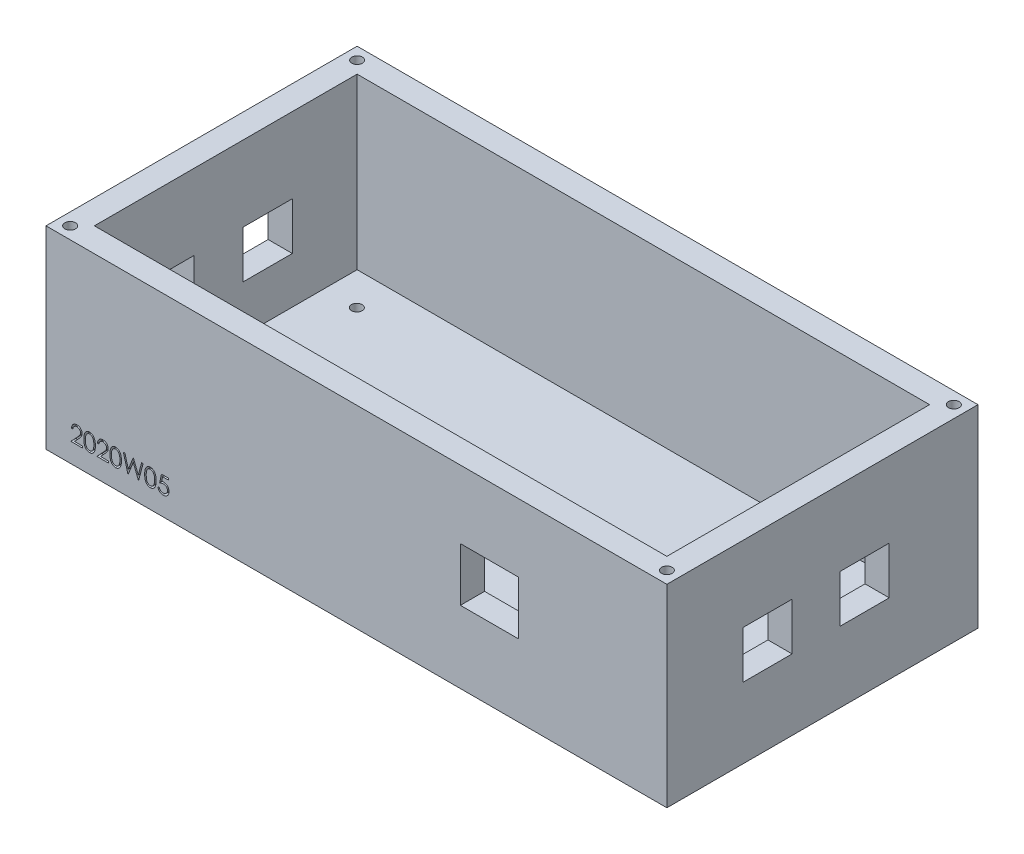
SolidWorks part; units mm, degrees
ref_plane "Front Plane" through (0, 0, 0) normal (0, 0, 1) x (1, 0, 0)
ref_plane "Top Plane" through (0, 0, 0) normal (0, 1, 0) x (1, 0, 0)
ref_plane "Right Plane" through (0, 0, 0) normal (1, 0, 0) x (0, 0, -1)
sketch "Sketch1" plane through (0, 0, 0) normal (0, 1, 0) x (1, 0, 0)
  line L0 (0, 0) -> (-128.3, 0)
  line L1 (-128.3, 0) -> (-128.3, 64.29)
  line L2 (-128.3, 64.29) -> (0, 64.29)
  line L3 (0, 64.29) -> (0, 0)
  dimension "D1" = 128.3
  dimension "D2" = 64.29
extrude "Boss-Extrude1" add sketch "Sketch1" along normal blind 5
sketch "Sketch2" plane through (0, 5, 0) normal (0, 1, 0) x (1, 0, 0)
  line L0 (-128.3, 64.29) -> (-128.3, 0)
  line L1 (-128.3, 0) -> (0, 0)
  line L2 (0, 0) -> (0, 64.29)
  line L3 (0, 64.29) -> (-128.3, 64.29)
  line L4 (-123.3, 59.29) -> (-123.3, 5)
  line L5 (-123.3, 5) -> (-5, 5)
  line L6 (-5, 5) -> (-5, 59.29)
  line L7 (-5, 59.29) -> (-123.3, 59.29)
  line L8 (-123.3, 59.29) -> (-123.3, 64.29) construction
  line L9 (-123.3, 59.29) -> (-128.3, 59.29) construction
  line L10 (-5, 59.29) -> (0, 59.29) construction
  line L11 (-5, 5) -> (-5, 0) construction
  dimension "D1" = 5
  dimension "D2" = 5
extrude "Boss-Extrude2" add sketch "Sketch2" along normal blind 35
sketch "Sketch3" plane through (0, 5, 0) normal (0, 1, 0) x (1, 0, 0)
  line L0 (-116.54, 52.465) -> (-11.76, 52.465) construction
  line L1 (-11.76, 52.465) -> (-11.76, 11.825) construction
  line L2 (-11.76, 11.825) -> (-116.54, 11.825) construction
  line L3 (-116.54, 11.825) -> (-116.54, 52.465) construction
  line L4 (-123.3, 52.465) -> (-116.54, 52.465) construction
  line L5 (-123.3, 59.29) -> (-123.3, 5) construction
  line L6 (-116.54, 52.465) -> (-116.54, 59.29) construction
  line L7 (-5, 59.29) -> (-123.3, 59.29) construction
  line L8 (-11.76, 52.465) -> (-5, 52.465) construction
  line L9 (-5, 5) -> (-5, 59.29) construction
  line L10 (-116.54, 11.825) -> (-116.54, 5) construction
  line L11 (-123.3, 5) -> (-5, 5) construction
  circle A0 centre (-116.54, 52.465) radius 1.1
  circle A1 centre (-11.76, 52.465) radius 1.1
  circle A2 centre (-11.76, 11.825) radius 1.1
  circle A3 centre (-116.54, 11.825) radius 1.1
  dimension "D1" = 2.2
  dimension "D2" = 104.78
  dimension "D3" = 40.64
extrude "Cut-Extrude1" cut sketch "Sketch3" against normal through all
sketch "Sketch4" plane through (0, 40, 0) normal (0, 1, 0) x (1, 0, 0)
  line L0 (-2.5, 61.79) -> (-125.8, 61.79) construction
  line L1 (-125.8, 61.79) -> (-125.8, 2.5) construction
  line L2 (-125.8, 2.5) -> (-2.5, 2.5) construction
  line L3 (-2.5, 2.5) -> (-2.5, 61.79) construction
  line L4 (-123.3, 59.29) -> (-125.8, 59.29) construction
  line L5 (-125.8, 59.29) -> (-128.3, 59.29) construction
  line L6 (-128.3, 64.29) -> (-128.3, 0) construction
  line L7 (-5, 59.29) -> (-2.5, 59.29) construction
  line L8 (-5, 5) -> (-5, 59.29) construction
  line L9 (-5, 5) -> (-5, 59.29) construction
  line L10 (-2.5, 59.29) -> (0, 59.29) construction
  line L11 (0, 0) -> (0, 64.29) construction
  line L12 (-123.3, 59.29) -> (-123.3, 61.79) construction
  line L13 (-123.3, 61.79) -> (-123.3, 64.29) construction
  line L14 (0, 64.29) -> (-128.3, 64.29) construction
  line L15 (-123.3, 5) -> (-123.3, 2.5) construction
  line L16 (-123.3, 2.5) -> (-123.3, 0) construction
  line L17 (-128.3, 0) -> (0, 0) construction
  circle A0 centre (-125.8, 61.79) radius 1.1
  circle A1 centre (-125.8, 2.5) radius 1.1
  circle A2 centre (-2.5, 2.5) radius 1.1
  circle A3 centre (-2.5, 61.79) radius 1.1
  dimension "D1" = 2.2
extrude "Cut-Extrude2" cut sketch "Sketch4" against normal blind 5
sketch "Sketch5" plane through (-128.3, 0, 0) normal (-1, 0, 0) x (0, 0, 1)
  line L0 (-45.9, 24.4) -> (-45.9, 14.6)
  line L1 (-45.9, 14.6) -> (-35.74, 14.6)
  line L2 (-35.74, 14.6) -> (-35.74, 24.4)
  line L3 (-35.74, 24.4) -> (-45.9, 24.4)
  line L4 (-25.58, 24.4) -> (-25.58, 14.6)
  line L5 (-25.58, 14.6) -> (-15.42, 14.6)
  line L6 (-15.42, 14.6) -> (-15.42, 24.4)
  line L7 (-25.58, 24.4) -> (-15.42, 24.4)
  line L8 (-64.29, 40) -> (-64.29, 0) construction
  line L9 (-64.29, 0) -> (0, 0) construction
  dimension "D1" = 10.16
  dimension "D2" = 10.16
  dimension "D3" = 10.16
  dimension "D4" = 18.39
  dimension "D5" = 9.8
  dimension "D6" = 14.6
extrude "Cut-Extrude3" cut sketch "Sketch5" against normal blind 61
sketch "Sketch6" plane through (0, 0, 0) normal (1, 0, 0) x (0, 0, -1)
  line L0 (15.72, 24.4) -> (15.72, 14.6)
  line L1 (15.72, 14.6) -> (25.88, 14.6)
  line L2 (25.88, 14.6) -> (25.88, 24.4)
  line L3 (25.88, 24.4) -> (15.72, 24.4)
  line L4 (35.79, 24.4) -> (35.79, 14.6)
  line L5 (35.79, 14.6) -> (45.95, 14.6)
  line L6 (45.95, 14.6) -> (45.95, 24.4)
  line L7 (45.95, 24.4) -> (35.79, 24.4)
  line L8 (0, 0) -> (64.29, 0) construction
  line L9 (0, 40) -> (0, 0) construction
  dimension "D1" = 10.16
  dimension "D2" = 10.16
  dimension "D3" = 9.91
  dimension "D4" = 9.8
  dimension "D5" = 14.6
  dimension "D6" = 15.72
extrude "Cut-Extrude4" cut sketch "Sketch6" against normal blind 61
sketch "Sketch7" plane through (0, 0, 0) normal (0, 0, 1) x (1, 0, 0)
  line L0 (-42.67, 25.95) -> (-42.67, 14.9)
  line L1 (-42.67, 14.9) -> (-30.64, 14.9)
  line L2 (-30.64, 14.9) -> (-30.64, 25.95)
  line L3 (-30.64, 25.95) -> (-42.67, 25.95)
  line L6 (-128.3, 0) -> (0, 0) construction
  line L7 (0, 40) -> (0, 0) construction
  dimension "D1" = 12.03
  dimension "D2" = 11.05
  dimension "D3" = 14.9
  dimension "D4" = 30.64
extrude "Cut-Extrude5" cut sketch "Sketch7" against normal blind 35
sketch "Sketch8" plane through (0, 0, 0) normal (0, 0, 1) x (1, 0, 0)
  line L0 (-128.3, 0) -> (0, 0) construction
  line L1 (-128.3, 40) -> (-128.3, 0) construction
  text T0 "2020W05"
  dimension "D1" = 4
  dimension "D2" = 5
extrude "Cut-Extrude6" cut sketch "Sketch8" against normal blind 1
